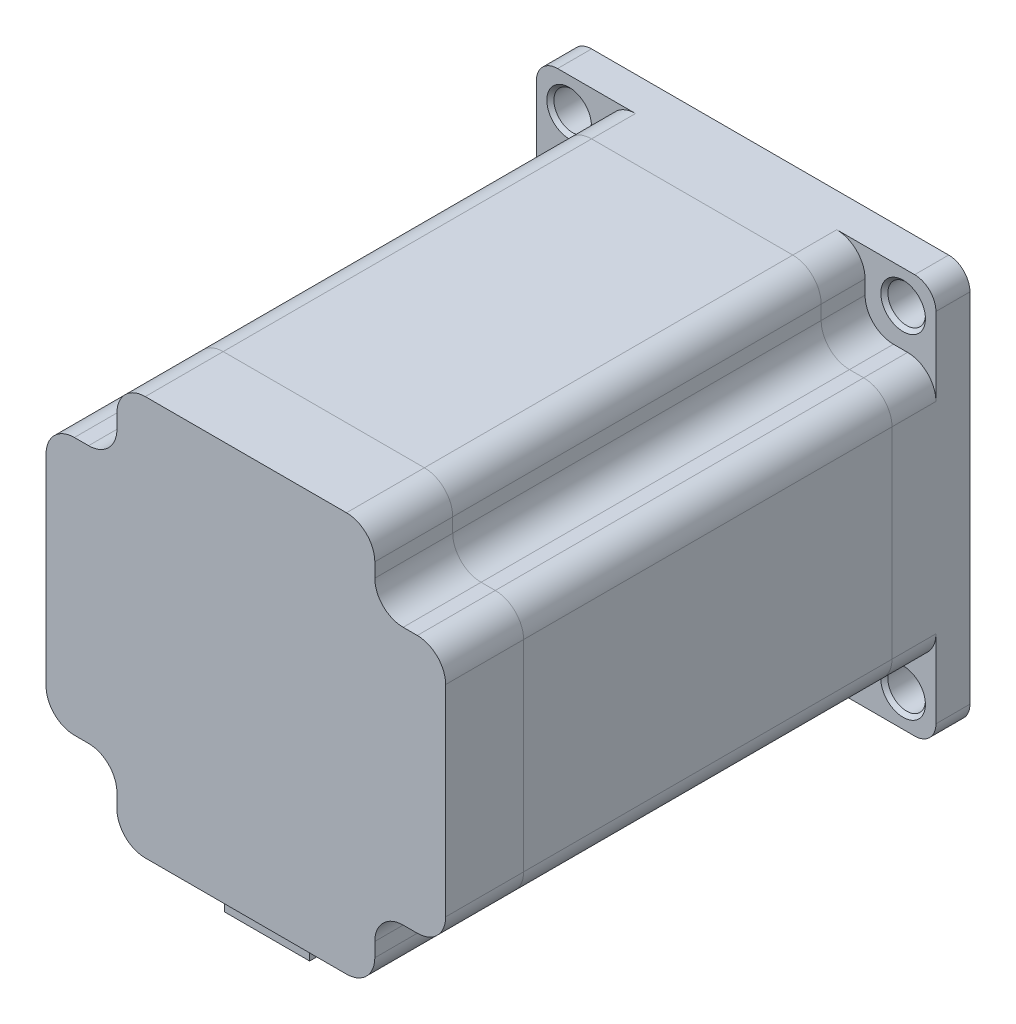
SolidWorks part; units mm, degrees
material "6061 合金"
ref_plane "前基準面" through (0, 0, 0) normal (0, 0, 1) x (1, 0, 0)
ref_plane "上基準面" through (0, 0, 0) normal (0, 1, 0) x (1, 0, 0)
ref_plane "右基準面" through (0, 0, 0) normal (1, 0, 0) x (0, 0, -1)
sketch "草圖1" plane through (0, 0, 0) normal (0, 0, 1) x (1, 0, 0)
  line L1 (-28.2, -28.2) -> (28.2, -28.2)
  line L2 (-28.2, -28.2) -> (-28.2, 28.2)
  line L3 (-28.2, 28.2) -> (28.2, 28.2)
  line L4 (28.2, -28.2) -> (28.2, 28.2)
  line L5 (-28.2, -28.2) -> (28.2, 28.2) construction
  line L6 (-28.2, 28.2) -> (28.2, -28.2) construction
  point P0 (0, 0)
  dimension "D1" = 56.4
extrude "填料-伸長1" add sketch "草圖1" along normal blind 11
sketch "草圖2" plane through (0, 0, 11) normal (0, 0, 1) x (1, 0, 0)
  line L1 (-28.2, -28.2) -> (28.2, -28.2)
  line L2 (-28.2, -28.2) -> (-28.2, 28.2)
  line L3 (-28.2, 28.2) -> (28.2, 28.2)
  line L4 (28.2, -28.2) -> (28.2, 28.2)
  line L5 (-28.2, -28.2) -> (28.2, 28.2) construction
  line L6 (-28.2, 28.2) -> (28.2, -28.2) construction
  point P0 (0, 0)
extrude "填料-伸長2" add sketch "草圖2" along normal blind 52 separate body
sketch "草圖3" plane through (0, 0, 63) normal (0, 0, 1) x (1, 0, 0)
  line L1 (-28.2, -28.2) -> (28.2, -28.2)
  line L2 (-28.2, -28.2) -> (-28.2, 28.2)
  line L3 (-28.2, 28.2) -> (28.2, 28.2)
  line L4 (28.2, -28.2) -> (28.2, 28.2)
  line L5 (-28.2, -28.2) -> (28.2, 28.2) construction
  line L6 (-28.2, 28.2) -> (28.2, -28.2) construction
  point P0 (0, 0)
extrude "填料-伸長3" add sketch "草圖3" along normal blind 11 separate body
sketch "草圖4" plane through (0, 0, 0) normal (0, 0, -1) x (-1, 0, 0)
  circle A0 centre (0, 0) radius 19.05
  dimension "D1" = 38.1
extrude "填料-伸長4" add sketch "草圖4" along normal blind 1.6
sketch "草圖5" plane through (0, 0, -1.6) normal (0, 0, -1) x (-1, 0, 0)
  circle A0 centre (0, 0) radius 5
  dimension "D1" = 10
extrude "除料-伸長1" cut sketch "草圖5" against normal blind 5
sketch "草圖6" plane through (0, 0, 3.4) normal (0, 0, -1) x (-1, 0, 0)
  circle A0 centre (0, 0) radius 3.175
  dimension "D1" = 6.35
extrude "填料-伸長5" add sketch "草圖6" along normal offset from surface (25.4 mm away) 22 separate body up to face at (-19.05, 0, 0) offset beyond the face yes
sketch "草圖7" plane through (0, 0, -22) normal (0, 0, -1) x (-1, 0, 0)
  line L0 (-1.7103, 2.675) -> (1.7103, 2.675)
  arc A0 (-1.7103, 2.675) -> (1.7103, 2.675) centre (0, 0) cw
  circle A1 centre (0, 0) radius 3.175 construction
  point P3 (0, 3.175)
  dimension "D1" = 0.5
extrude "除料-伸長2" cut sketch "草圖7" against normal blind 20
sketch "草圖8" plane through (0, 0, 74) normal (0, 0, 1) x (1, 0, 0)
  line L0 (28.2, 28.2) -> (-28.2, 28.2) construction
  line L1 (28.2, 28.2) -> (18.2, 28.2)
  line L2 (28.2, 28.2) -> (28.2, 18.2)
  line L3 (28.2, 18.2) -> (18.2, 18.2)
  line L4 (18.2, 28.2) -> (18.2, 18.2)
  line L5 (28.2, 28.2) -> (18.2, 18.2) construction
  line L6 (28.2, 18.2) -> (18.2, 28.2) construction
  point P4 (23.2, 23.2)
  dimension "D1" = 10
  dimension "D2" = 10
extrude "除料-伸長3" cut sketch "草圖8" against normal offset from surface (69.2 mm away) 4.8 up to face at (-19.05, 0, 0)
pattern_circular "環狀複製排列1" count 4 over 360 about axis through (0, 0, 0) along (0, 0, 1) of "除料-伸長3"
hole_wizard "M5 餘隙孔1" positions "草圖10" profile "草圖11" hole size "M5" standard "Ansi Metric" end condition through all
sketch "草圖10" plane through (0, 0, 4.8) normal (0, 0, 1) x (1, 0, 0)
  line L9 (-23.57, -23.57) -> (23.57, -23.57) construction
  line L10 (-23.57, -23.57) -> (-23.57, 23.57) construction
  line L11 (-23.57, 23.57) -> (23.57, 23.57) construction
  line L12 (23.57, -23.57) -> (23.57, 23.57) construction
  line L13 (-23.57, -23.57) -> (23.57, 23.57) construction
  line L14 (-23.57, 23.57) -> (23.57, -23.57) construction
  point P32 (23.57, 23.57)
  point P65 (-23.57, -23.57)
  point P66 (-23.57, 23.57)
  point P67 (23.57, -23.57)
  dimension "D1" = 47.14
  dimension "D2" = 47.14
sketch "草圖11" plane through (23.57, 23.57, 4.8) normal (1, 0, 0) x (0, -1, 0)
  line L0 (0, 0) -> (0, 26.8)
  line L1 (0, 26.8) -> (2.65, 26.8)
  line L2 (2.65, 26.8) -> (2.65, 0)
  line L5 (2.65, 0) -> (0, 0)
  line L11 (0, -6.35) -> (0, 107.95) construction
  dimension "貫穿孔直徑" = 5.3
  dimension "貫穿孔深度" = 26.8
chamfer "導角1" distance 0.5 angle 45 8 edges at (-20.92, 23.57, 4.8) (-26.22, 23.57, 0) (-20.92, -23.57, 4.8) (-26.22, -23.57, 0) (26.22, -23.57, 4.8) (20.92, -23.57, 0) (26.22, 23.57, 4.8) (20.92, 23.57, 0)
fillet "圓角1" radius 3 4 edges at (28.2, 28.2, 2.4) (28.2, -28.2, 2.4) (-28.2, -28.2, 2.4) (-28.2, 28.2, 2.4)
fillet "圓角2" radius 4 12 edges at (18.2, 18.2, 7.9) (28.2, 18.2, 7.9) (18.2, 28.2, 7.9) (28.2, -18.2, 7.9) (18.2, -18.2, 7.9) (18.2, -28.2, 7.9) (-18.2, -28.2, 7.9) (-18.2, -18.2, 7.9) (-28.2, -18.2, 7.9) (-28.2, 18.2, 7.9) (-18.2, 18.2, 7.9) (-18.2, 28.2, 7.9)
fillet "圓角3" radius 4 12 edges at (18.2, 18.2, 37) (28.2, 18.2, 37) (18.2, 28.2, 37) (28.2, -18.2, 37) (18.2, -18.2, 37) (18.2, -28.2, 37) (-18.2, -28.2, 37) (-18.2, -18.2, 37) (-28.2, -18.2, 37) (-28.2, 18.2, 37) (-18.2, 18.2, 37) (-18.2, 28.2, 37)
fillet "圓角4" radius 4 12 edges at (18.2, 18.2, 68.5) (28.2, 18.2, 68.5) (18.2, 28.2, 68.5) (28.2, -18.2, 68.5) (18.2, -18.2, 68.5) (18.2, -28.2, 68.5) (-18.2, -28.2, 68.5) (-18.2, -18.2, 68.5) (-28.2, -18.2, 68.5) (-28.2, 18.2, 68.5) (-18.2, 18.2, 68.5) (-18.2, 28.2, 68.5)
sketch "草圖12" plane through (0, -28.2, 0) normal (0, -1, 0) x (1, 0, 0)
  line L0 (0, 74) -> (0, 68.5) construction
  line L1 (-14.2, 74) -> (14.2, 74) construction
  line L3 (-6, 71) -> (6, 71)
  line L4 (-6, 71) -> (-6, 66)
  line L5 (-6, 66) -> (6, 66)
  line L6 (6, 71) -> (6, 66)
  line L7 (-6, 71) -> (6, 66) construction
  line L8 (-6, 66) -> (6, 71) construction
  dimension "D1" = 3
  dimension "D2" = 5
  dimension "D3" = 12
extrude "填料-伸長6" add sketch "草圖12" along normal blind 4 separate body
sketch "草圖13" plane through (0, 0, 66) normal (0, 0, -1) x (-1, 0, 0)
  line L0 (0, -28.2) -> (0, -32.2) construction
  line L2 (6, -28.2) -> (-6, -28.2) construction
  line L3 (6, -32.2) -> (-6, -32.2) construction
  line L4 (0, -30.2) -> (1.5, -30.2) construction
  circle A1 centre (1.5, -30.2) radius 0.8
  point P9 (0, -30.2)
  dimension "D2" = 1.6
  dimension "D1" = 1.5
extrude "填料-伸長7" add sketch "草圖13" along normal blind 10 separate body
pattern_linear "直線複製排列1" count 3 spacing 3 along (1, 0, 0) count 2 spacing 3 along (-1, 0, 0) of "填料-伸長7"
